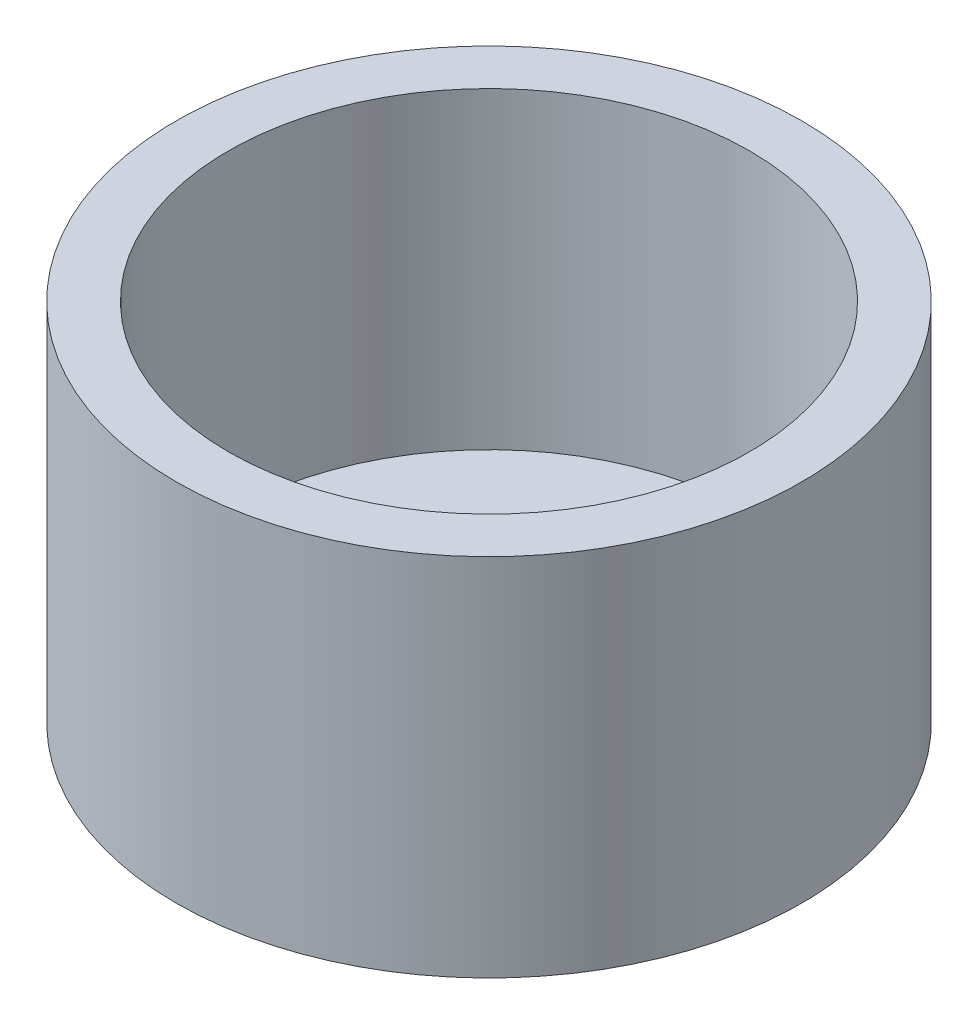
SolidWorks part; units mm, degrees
ref_plane "Front Plane" through (0, 0, 0) normal (0, 0, 1) x (1, 0, 0)
ref_plane "Top Plane" through (0, 0, 0) normal (0, 1, 0) x (1, 0, 0)
ref_plane "Right Plane" through (0, 0, 0) normal (1, 0, 0) x (0, 0, -1)
sketch "Sketch1" plane through (0, 0, 0) normal (0, 1, 0) x (1, 0, 0)
  circle A0 centre (-5.4251, 4.3107) radius 15
  dimension "D1" = 30
extrude "Boss-Extrude1" add sketch "Sketch1" along normal blind 17.5
sketch "Sketch2" plane through (0, 17.5, 0) normal (0, 1, 0) x (1, 0, 0)
  circle A0 centre (-5.4251, 4.3107) radius 12.5
  circle A1 centre (-5.4251, 4.3107) radius 15 construction
  dimension "D1" = 25
extrude "Cut-Extrude1" cut sketch "Sketch2" against normal blind 15
